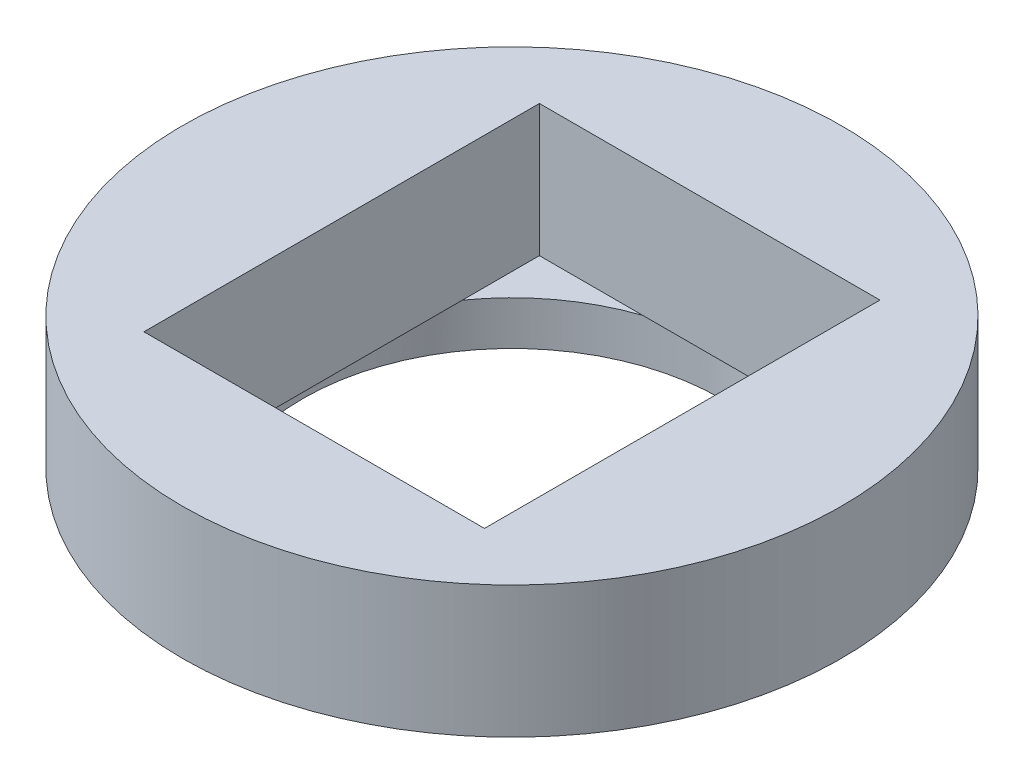
SolidWorks part; units mm, degrees
ref_plane "Plan de face" through (0, 0, 0) normal (0, 0, 1) x (1, 0, 0)
ref_plane "Plan de dessus" through (0, 0, 0) normal (0, 1, 0) x (1, 0, 0)
ref_plane "Plan de droite" through (0, 0, 0) normal (1, 0, 0) x (0, 0, -1)
sketch "Esquisse1" plane through (0, 0, 0) normal (0, 1, 0) x (1, 0, 0)
  circle A0 centre (0, 0) radius 11.975
  circle A1 centre (0, 0) radius 9.5
  dimension "D1" = 23.95
  dimension "D2" = 19
extrude "Boss.-Extru.1" add sketch "Esquisse1" along normal blind 2
sketch "Esquisse3" plane through (0, 2, 0) normal (0, 1, 0) x (1, 0, 0)
  line L5 (-7.75, -9) -> (7.75, -9)
  line L6 (-7.75, -9) -> (-7.75, 9)
  line L7 (-7.75, 9) -> (7.75, 9)
  line L8 (7.75, -9) -> (7.75, 9)
  line L9 (-7.75, -9) -> (7.75, 9) construction
  line L10 (-7.75, 9) -> (7.75, -9) construction
  circle A0 centre (0, 0) radius 9.5 construction
  circle A1 centre (0, 0) radius 9.5 construction
  circle A2 centre (0, 0) radius 15
  point P0 (0, 0)
  dimension "D3" = 18
  dimension "D1" = 30
  dimension "D2" = 15.5
extrude "Boss.-Extru.5" add sketch "Esquisse3" along normal blind 2 contours A2 | L6 L5 L8 L7
sketch "Esquisse8" plane through (0, 4, 0) normal (0, 1, 0) x (1, 0, 0)
  line L0 (-7.75, -9) -> (7.75, -9) construction
  line L1 (-8.45, 2.55) -> (-13.55, 2.55) construction
  line L2 (-8.45, 2.55) -> (-8.45, -2.55) construction
  line L3 (-8.45, -2.55) -> (-13.55, -2.55) construction
  line L4 (-13.55, 2.55) -> (-13.55, -2.55) construction
  line L5 (-8.45, 2.55) -> (-13.55, -2.55) construction
  line L6 (-8.45, -2.55) -> (-13.55, 2.55) construction
  line L7 (13.55, 2.55) -> (8.45, 2.55) construction
  line L8 (13.55, 2.55) -> (13.55, -2.55) construction
  line L9 (13.55, -2.55) -> (8.45, -2.55) construction
  line L10 (8.45, 2.55) -> (8.45, -2.55) construction
  line L11 (13.55, 2.55) -> (8.45, -2.55) construction
  line L12 (13.55, -2.55) -> (8.45, 2.55) construction
  line L13 (7.75, -9) -> (7.75, 9) construction
  line L14 (-7.75, 9) -> (7.75, 9) construction
  line L15 (-7.75, 9) -> (-3.0414, 9) construction
  line L16 (-7.75, -9) -> (-7.75, 9) construction
  line L17 (-7.75, -9) -> (7.75, -9)
  line L18 (7.75, -9) -> (7.75, 9)
  line L19 (-7.75, 9) -> (7.75, 9)
  line L20 (-7.75, 9) -> (-3.0414, 9)
  line L21 (-7.75, -9) -> (-7.75, 9)
  circle A1 centre (0, 0) radius 15
  circle A2 centre (0, 0) radius 15
  point P0 (-11, 0)
  point P5 (11, 0)
  line M11 (-7.75, 9) -> (7.75, 9)
  line M12 (7.75, 9) -> (7.75, -9)
  line M13 (7.75, -9) -> (-7.75, -9)
  line M14 (-7.75, -9) -> (-7.75, 9)
  circle M15 centre (0, 0) radius 15
  dimension "D1" = 5.1
  dimension "D2" = 11
  dimension "D3" = 11
  dimension "D4" = 0
extrude "Boss.-Extru.6" add sketch "Esquisse8" along normal blind 4 contours L10 L7 L8 L9 L4 L1 L2 L3 L19 M15 M14 M11 M12 M13
